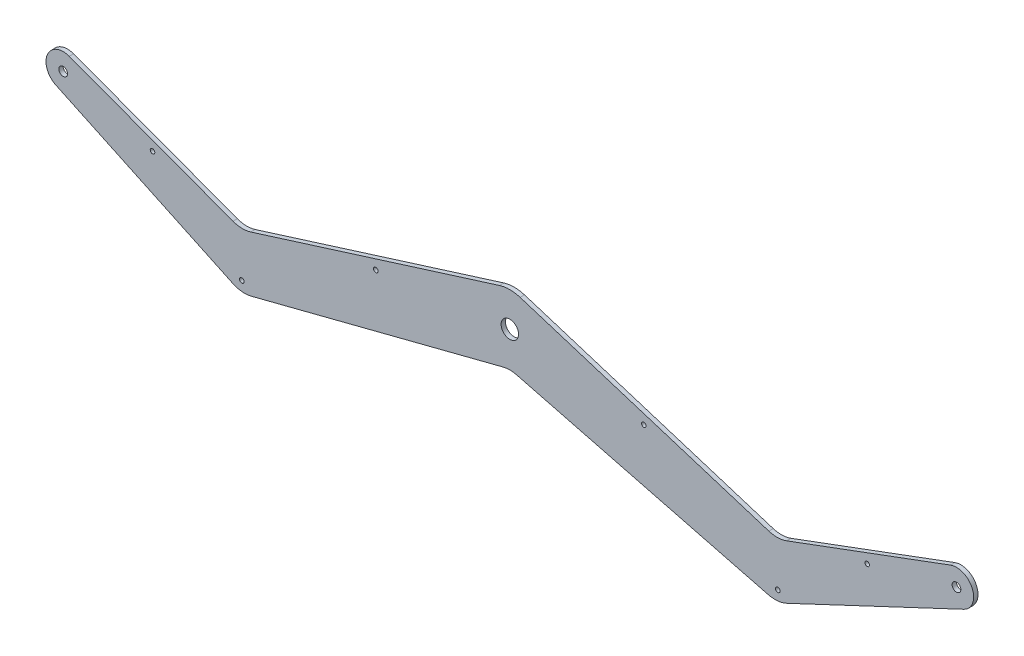
SolidWorks part; units mm, degrees
ref_plane "Front Plane" through (0, 0, 0) normal (0, 0, 1) x (1, 0, 0)
ref_plane "Top Plane" through (0, 0, 0) normal (0, 1, 0) x (1, 0, 0)
ref_plane "Right Plane" through (0, 0, 0) normal (1, 0, 0) x (0, 0, -1)
sketch "Sketch1" plane through (0, 0, 0) normal (0, 0, 1) x (1, 0, 0)
  line L0 (-7.4864, 23.8528) -> (-188.4628, -32.9483)
  line L1 (-4.9675, -26.2737) -> (-188.028, -73.2123)
  line L2 (-325, 0) -> (0, 0) construction
  line L3 (-320.6437, 11.7163) -> (-201.422, -32.6122)
  line L4 (-330.3231, -11.31) -> (-201.5123, -71.935)
  line L5 (-195, -35) -> (-195, -75) construction
  line L6 (-195, -35) -> (-195, 0) construction
  line L7 (0, -25) -> (0, 25) construction
  line L8 (4.9675, -26.2737) -> (188.028, -73.2123)
  line L9 (7.4864, 23.8528) -> (188.4628, -32.9483)
  line L10 (330.3231, -11.31) -> (201.5123, -71.935)
  line L11 (320.6437, 11.7163) -> (201.422, -32.6122)
  arc A0 (7.4864, 23.8528) -> (-7.4864, 23.8528) centre (0, 0) ccw
  arc A1 (-320.6437, 11.7163) -> (-330.3231, -11.31) centre (-325, 0) ccw
  arc A2 (320.6437, 11.7163) -> (330.3231, -11.31) centre (325, 0) cw
  arc A3 (188.028, -73.2123) -> (201.5123, -71.935) centre (192.9955, -53.839) ccw
  arc A4 (188.4628, -32.9483) -> (201.422, -32.6122) centre (194.4519, -13.866) ccw
  arc A5 (-188.4628, -32.9483) -> (-201.422, -32.6122) centre (-194.4519, -13.866) cw
  arc A6 (-188.028, -73.2123) -> (-201.5123, -71.935) centre (-192.9955, -53.839) cw
  arc A7 (-4.9675, -26.2737) -> (4.9675, -26.2737) centre (0, -45.647) cw
  point P19 (195, -75)
  point P22 (195, -35)
  dimension "D2" = 25
  dimension "D1" = 25
  dimension "D6" = 20
  dimension "D7" = 20
  dimension "Half of Chassis Width" = 325
  dimension "D3" = 35
  dimension "D4" = 40
  dimension "Quarter Chassis Width" = 195
  dimension "D5" = 50
extrude "Boss-Extrude1" add sketch "Sketch1" along normal blind 3.18
sketch "Sketch2" plane through (0, 0, 3.18) normal (0, 0, 1) x (1, 0, 0)
  line L0 (-325, 0) -> (0, 0) construction
  line L1 (-260, 0) -> (-260, -17.832) construction
  line L2 (-195, 0) -> (-195, -66.7383) construction
  line L3 (-97.5, 0) -> (-97.5, -11.3988) construction
  line L4 (-260, -17.832) -> (-260, -10.832) construction
  line L5 (-201.422, -32.6122) -> (-320.6437, 11.7163) construction
  line L6 (-195, -66.7383) -> (-195, -73.7383) construction
  line L7 (-97.5, -11.3988) -> (-97.5, -4.3988) construction
  line L8 (-7.4864, 23.8528) -> (-188.4628, -32.9483) construction
  line L9 (0, -25.647) -> (0, 25) construction
  circle A0 centre (0, 0) radius 6.35
  circle A1 centre (-325, 0) radius 3.175
  circle A2 centre (-97.5, -11.3988) radius 1.65
  circle A3 centre (-195, -66.7383) radius 1.65
  circle A4 centre (-260, -17.832) radius 1.65
  arc A5 (-201.5123, -71.935) -> (-188.028, -73.2123) centre (-192.9955, -53.839) ccw construction
  arc A6 (4.9675, -26.2737) -> (-4.9675, -26.2737) centre (0, -45.647) ccw construction
  arc A7 (7.4864, 23.8528) -> (-7.4864, 23.8528) centre (0, 0) ccw construction
  circle A8 centre (97.5, -11.3988) radius 1.65
  circle A9 centre (195, -66.7383) radius 1.65
  circle A10 centre (260, -17.832) radius 1.65
  circle A11 centre (325, 0) radius 3.175
  dimension "D1" = 12.7
  dimension "D2" = 6.35
  dimension "D3" = 3.3
  dimension "Hole3" = 260
  dimension "Hole2" = 195
  dimension "Hole1" = 97.5
  dimension "D4" = 7
  dimension "D5" = 7
  dimension "D6" = 7
extrude "Cut-Extrude1" cut sketch "Sketch2" against normal through all
equation "\"Half of Chassis Width@Sketch1\"= \"Chassis Width@Differential System Assy - Option 2.Assembly\" / 2"
equation "\"Quarter Chassis Width@Sketch1\"= \"Chassis Width@Differential System Assy - Option 2.Assembly\" / 2 * 0.6"
equation "\"Hole3@Sketch2\"= \"Chassis Width@Differential System Assy - Option 2.Assembly\" / 2 * 0.8"
equation "\"Hole2@Sketch2\"= \"Chassis Width@Differential System Assy - Option 2.Assembly\" / 2 * 0.6"
equation "\"Hole1@Sketch2\"= \"Chassis Width@Differential System Assy - Option 2.Assembly\" / 2 * 0.3"
